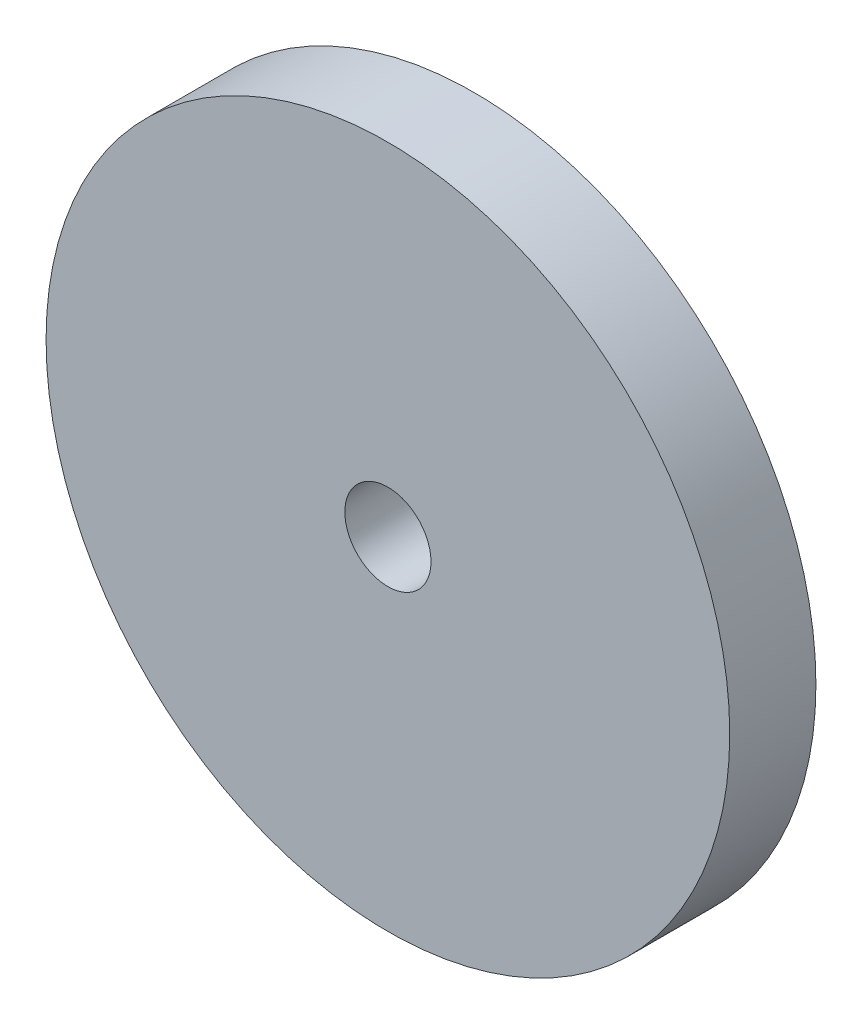
SolidWorks part; units mm, degrees
ref_plane "Alzado" through (0, 0, 0) normal (0, 0, 1) x (1, 0, 0)
ref_plane "Planta" through (0, 0, 0) normal (0, 1, 0) x (1, 0, 0)
ref_plane "Vista lateral" through (0, 0, 0) normal (1, 0, 0) x (0, 0, -1)
sketch "Model" plane through (0, 0, 0) normal (0, 0, 1) x (1, 0, 0)
  circle A0 centre (55, 31) radius 1.5
  circle A1 centre (55, 31) radius 11.9
extrude "Saliente-Extruir1" add sketch "Model" along normal blind 3
